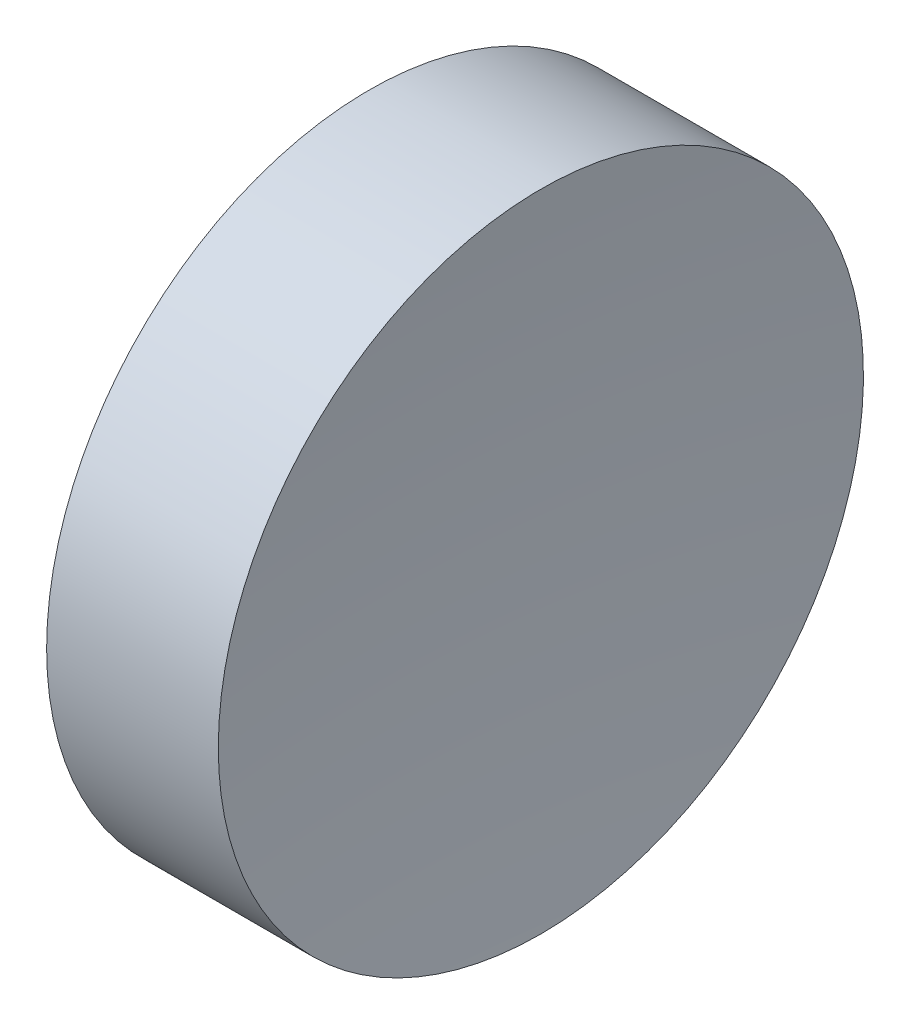
SolidWorks part; units mm, degrees
ref_plane "前视基准面" through (0, 0, 0) normal (0, 0, 1) x (1, 0, 0)
ref_plane "上视基准面" through (0, 0, 0) normal (0, 1, 0) x (1, 0, 0)
ref_plane "右视基准面" through (0, 0, 0) normal (1, 0, 0) x (0, 0, -1)
sketch "草图1" plane through (0, 0, 0) normal (0, 0, 1) x (1, 0, 0)
  line L0 (54.4926, 34.689) -> (66.3882, 34.689) construction
  line L1 (57.5463, 34.689) -> (57.5463, 40.939)
  line L2 (57.5463, 40.939) -> (60.8727, 40.939)
  line L3 (60.5463, 34.689) -> (57.5463, 34.689)
  arc A0 (60.8727, 40.939) -> (60.5463, 34.689) centre (120.5463, 34.689) ccw
  dimension "D1" = 3.3264
revolve "旋转1" add sketch "草图1" angle 360 about L0
